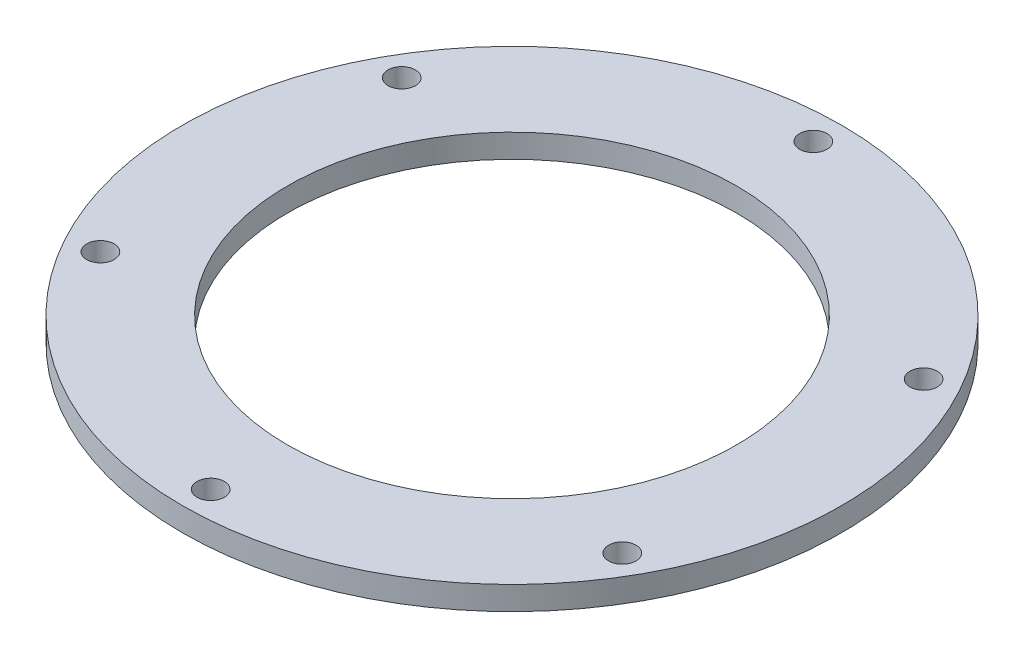
SolidWorks part; units mm, degrees
ref_plane "Front Plane" through (0, 0, 0) normal (0, 0, 1) x (1, 0, 0)
ref_plane "Top Plane" through (0, 0, 0) normal (0, 1, 0) x (1, 0, 0)
ref_plane "Right Plane" through (0, 0, 0) normal (1, 0, 0) x (0, 0, -1)
sketch "Sketch1" plane through (0, 0, 0) normal (0, 1, 0) x (1, 0, 0)
  circle A0 centre (0, 0) radius 40.64 construction
  circle A1 centre (0, 0) radius 44.45
  circle A2 centre (0, 0) radius 30.2759
  dimension "D1" = 81.28
  dimension "D2" = 88.9
  dimension "D3" = 60.5518
extrude "Boss-Extrude1" add sketch "Sketch1" along normal blind 3.175
hole_wizard "#6 Clearance Hole1" positions "Sketch2" profile "Sketch3" hole size "#6" standard "ANSI Inch" end condition up to next
sketch "Sketch2" plane through (0, 3.175, 0) normal (0, 1, 0) x (1, 0, 0)
  line L0 (0, 0) -> (0, 40.64) construction
  circle A0 centre (0, 0) radius 40.64
  point P0 (0, 40.64)
  dimension "D1" = 81.28
sketch "Sketch3" plane through (0, 3.175, -40.64) normal (1, 0, 0) x (0, 0, 1)
  line L0 (0, 0) -> (0, 3.176)
  line L1 (0, 3.176) -> (1.8478, 3.176)
  line L2 (1.8478, 3.176) -> (1.8478, 0)
  line L5 (1.8478, 0) -> (0, 0)
  line L11 (0, -6.35) -> (0, 107.95) construction
  dimension "Thru Hole Dia." = 3.6957
  dimension "Thru Hole Depth" = 3.176
pattern_circular "CirPattern1" count 6 over 360 about axis through (0, 0, 0) along (0, 1, 0) of "#6 Clearance Hole1"
